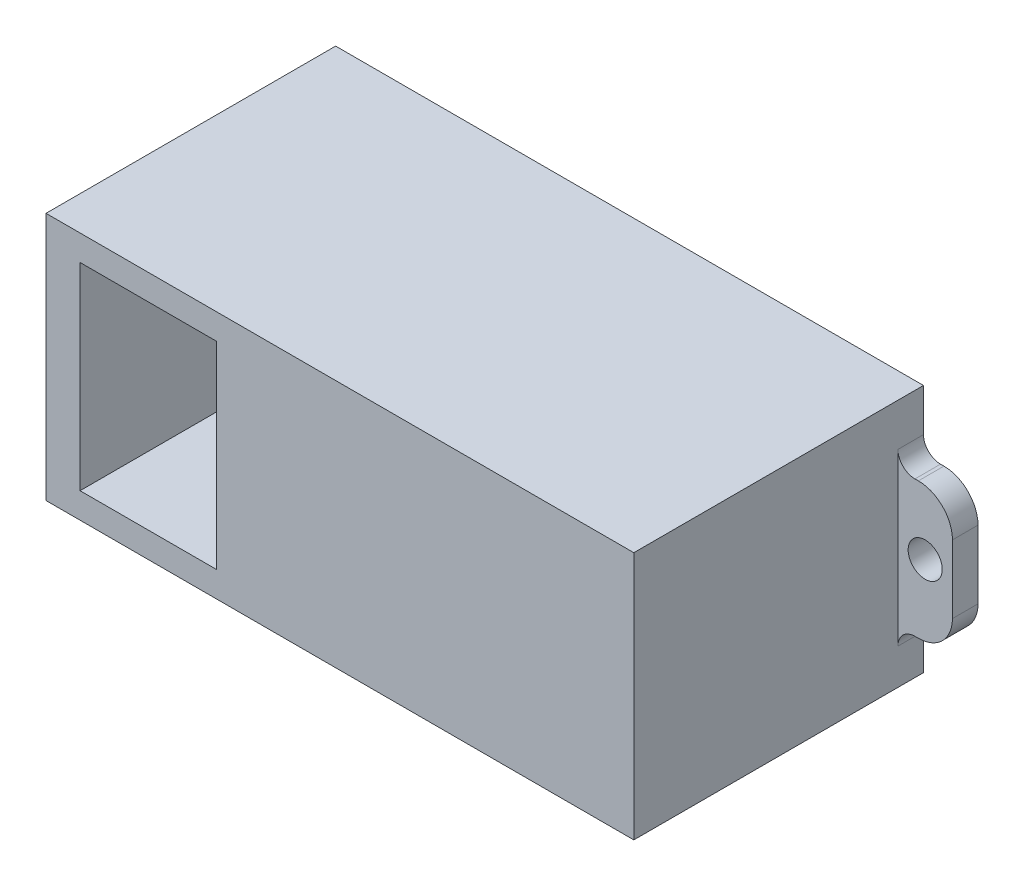
SolidWorks part; units mm, degrees
ref_plane "Ebene vorne" through (0, 0, 0) normal (0, 0, 1) x (1, 0, 0)
ref_plane "Ebene oben" through (0, 0, 0) normal (0, 1, 0) x (1, 0, 0)
ref_plane "Ebene rechts" through (0, 0, 0) normal (1, 0, 0) x (0, 0, -1)
sketch "Sketch1" plane through (0, 0, 0) normal (0, 0, 1) x (1, 0, 0)
  line L1 (11.25, -6.3) -> (-11.25, -6.3)
  line L2 (11.25, -6.3) -> (11.25, 6.3)
  line L3 (11.25, 6.3) -> (-11.25, 6.3)
  line L4 (-11.25, -6.3) -> (-11.25, 6.3)
  line L5 (11.25, -6.3) -> (-11.25, 6.3) construction
  line L6 (11.25, 6.3) -> (-11.25, -6.3) construction
  point P0 (0, 0)
  dimension "D1" = 12.6
  dimension "D2" = 22.5
extrude "Boss-Extrude1" add sketch "Sketch1" along normal blind 16
shell "Shell2" thickness 1
sketch "Sketch2" plane through (0, 0, 0) normal (0, 0, -1) x (-1, 0, 0)
  line L0 (-12.25, -7.3) -> (-12.25, 7.3) construction
  line L1 (-13.25, -4.2) -> (-13.45, -4.2)
  line L3 (-13.25, 3.8) -> (-13.45, 3.8)
  line L4 (-15.45, -2.2) -> (-15.45, 1.8)
  line L7 (-12.25, 7.3) -> (12.25, 7.3) construction
  line L9 (-12.25, -7.3) -> (-12.25, -5.2)
  line L10 (-12.25, 4.8) -> (-12.25, 7.3)
  line L11 (-11.25, 6.3) -> (11.25, 6.3) construction
  arc A0 (-15.45, -2.2) -> (-13.45, -4.2) centre (-13.45, -2.2) ccw
  arc A1 (-13.45, 3.8) -> (-15.45, 1.8) centre (-13.45, 1.8) ccw
  arc A2 (-13.25, 3.8) -> (-12.25, 4.8) centre (-13.25, 4.8) ccw
  arc A3 (-12.25, -5.2) -> (-13.25, -4.2) centre (-13.25, -5.2) ccw
  circle A4 centre (-13.85, 0) radius 1
  point P10 (-15.45, -4.2)
  point P13 (-15.45, 3.8)
  point P16 (-12.25, 3.8)
  point P19 (-12.25, -4.2)
  line M13 (-12.25, 7.3) -> (-12.25, -7.3)
  dimension "D4" = 2
  dimension "D5" = 1
  dimension "D6" = 1
  dimension "D8" = 2
  dimension "D1" = 8
  dimension "D2" = 3.5
  dimension "D3" = 1.6
  dimension "D7" = 6.3
  dimension "D9" = 1.6
extrude "Boss-Extrude2" add sketch "Sketch2" against normal blind 1.5 contours A3 A2 L3 A1 L4 A0 L1 A4 M13
sketch "Sketch4" plane through (0, 0, 0) normal (0, 0, -1) x (-1, 0, 0)
  line L0 (0, 9.0348) -> (0, -8.7607) construction
ref_plane "Plane1" through (0, 0, 0) normal (1, 0, 0) x (0, 0, -1)
mirror "Mirror1" about plane through (0, 0, 0) normal (1, 0, 0) of "Boss-Extrude2"
sketch "Sketch5" plane through (-12.25, 0, 0) normal (-1, 0, 0) x (0, 0, 1)
  line L0 (17, 7.3) -> (0, 7.3) construction
  line L1 (0, 5.8) -> (17, 5.8)
  line L2 (0, 5.8) -> (0, 7.3)
  line L3 (0, 7.3) -> (17, 7.3)
  line L4 (17, 5.8) -> (17, 7.3)
  line L6 (0, -5.8) -> (17, -5.8)
  line L7 (0, -5.8) -> (0, -7.3)
  line L8 (0, -7.3) -> (17, -7.3)
  line L9 (17, -5.8) -> (17, -7.3)
  point P13 (0, 0)
  point P15 (0, 0)
  dimension "D1" = 1.5
  dimension "D2" = 1.5
extrude "Boss-Extrude3" add sketch "Sketch5" along normal blind 10
sketch "Sketch6" plane through (-22.25, 0, 0) normal (-1, 0, 0) x (0, 0, 1)
  line L0 (17, -5.8) -> (0, -5.8) construction
  line L1 (0, 5.8) -> (17, 5.8)
  line L2 (0, 5.8) -> (0, -5.8)
  line L3 (0, -5.8) -> (17, -5.8)
  line L4 (17, 5.8) -> (17, -5.8)
  line L5 (17, -5.8) -> (0, -5.8) construction
extrude "Boss-Extrude4" add sketch "Sketch6" against normal blind 2
